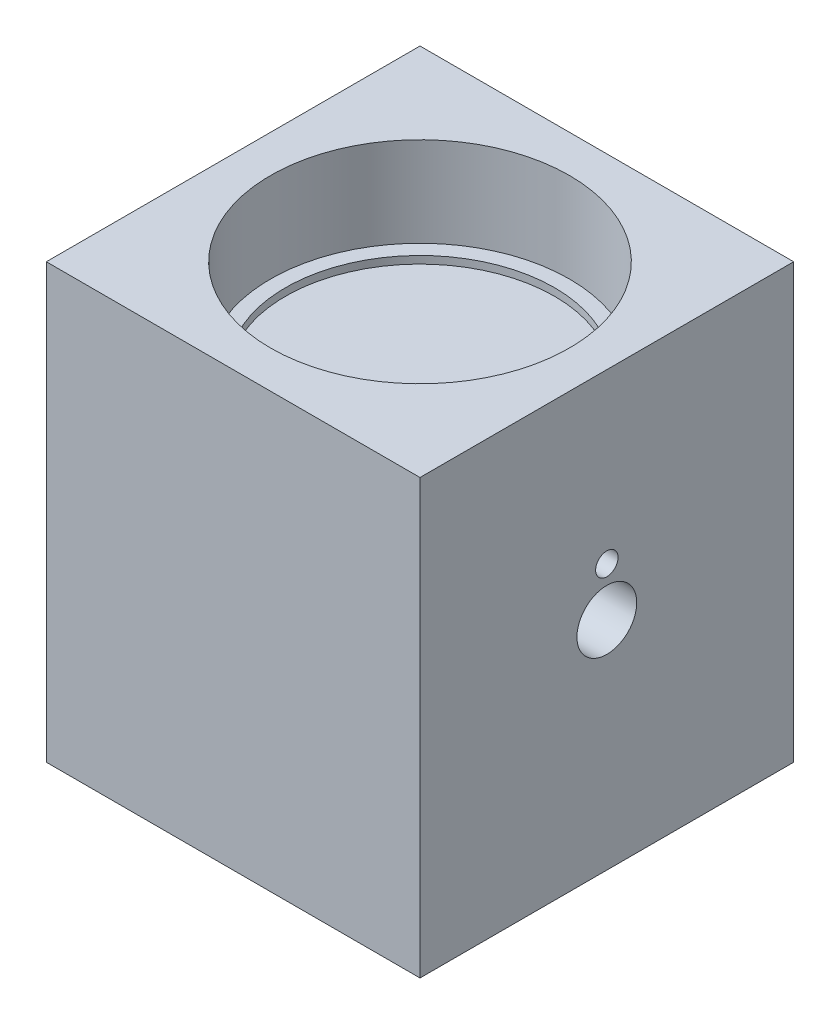
SolidWorks part; units mm, degrees
material "5052-H32"
ref_plane "Front Plane" through (0, 0, 0) normal (0, 0, 1) x (1, 0, 0)
ref_plane "Top Plane" through (0, 0, 0) normal (0, 1, 0) x (1, 0, 0)
ref_plane "Right Plane" through (0, 0, 0) normal (1, 0, 0) x (0, 0, -1)
sketch "Sketch1" plane through (0, 0, 0) normal (0, 1, 0) x (1, 0, 0)
  line L1 (-25, -25) -> (25, -25)
  line L2 (-25, -25) -> (-25, 25)
  line L3 (-25, 25) -> (25, 25)
  line L4 (25, -25) -> (25, 25)
  line L5 (-25, -25) -> (25, 25) construction
  line L6 (-25, 25) -> (25, -25) construction
  point P0 (0, 0)
  dimension "D1" = 50
extrude "Boss-Extrude1" add sketch "Sketch1" along normal mid plane 58
sketch "Sketch2" plane through (-25, 0, 0) normal (-1, 0, 0) x (0, 0, 1)
  line L0 (25, 0) -> (-25, 0) construction
  circle A0 centre (0, 0) radius 10
  dimension "D1" = 20
extrude "Cut-Extrude1" cut sketch "Sketch2" against normal blind 40
sketch "Sketch5" plane through (15, 0, 0) normal (-1, 0, 0) x (0, 0, 1)
  line L0 (0, 0) -> (0, 6.5) construction
  circle A0 centre (0, 6.5) radius 1.5
  circle A1 centre (0, 0) radius 4
  dimension "D1" = 3
  dimension "D3" = 8
  dimension "D2" = 6.5
extrude "Cut-Extrude2" cut sketch "Sketch5" against normal through all
sketch "Sketch6" plane through (0, 29, 0) normal (0, 1, 0) x (1, 0, 0)
  circle A0 centre (0, 0) radius 20
  dimension "D1" = 40
extrude "Cut-Extrude3" cut sketch "Sketch6" against normal blind 12
sketch "Sketch7" plane through (0, 17, 0) normal (0, 1, 0) x (1, 0, 0)
  circle A0 centre (0, 0) radius 18
  dimension "D1" = 36
extrude "Cut-Extrude4" cut sketch "Sketch7" against normal blind 1
mirror "Mirror1" about plane through (0, 0, 0) normal (0, 1, 0) of "Cut-Extrude4", "Cut-Extrude3"
